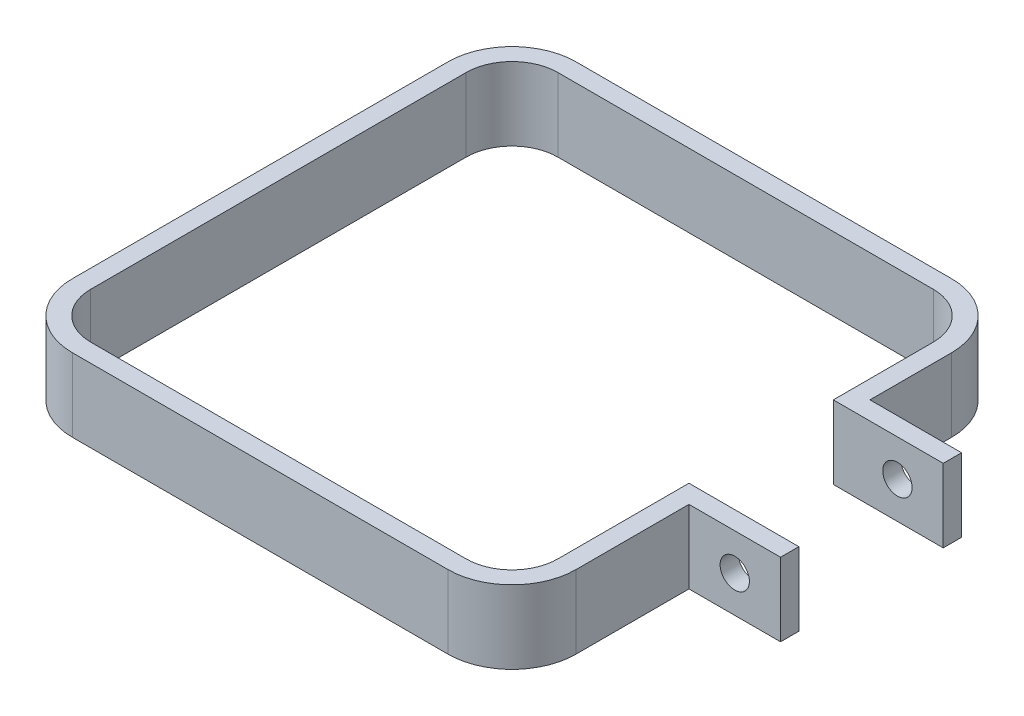
SolidWorks part; units mm, degrees
ref_plane "Front Plane" through (0, 0, 0) normal (0, 0, 1) x (1, 0, 0)
ref_plane "Top Plane" through (0, 0, 0) normal (0, 1, 0) x (1, 0, 0)
ref_plane "Right Plane" through (0, 0, 0) normal (1, 0, 0) x (0, 0, -1)
sketch "Sketch1" plane through (0, 0, 0) normal (0, 1, 0) x (1, 0, 0)
  line L0 (-20.5, 27.5) -> (20.5, 27.5)
  line L1 (-20.5, 25.5) -> (20.5, 25.5)
  line L2 (-25.5, 20.5) -> (-25.5, -20.5)
  line L3 (-20.5, -25.5) -> (20.5, -25.5)
  line L4 (25.5, 20.5) -> (25.5, 9.5842)
  line L5 (-25.5, 25.5) -> (25.5, -25.5) construction
  line L6 (-25.5, -25.5) -> (25.5, 25.5) construction
  line L7 (27.5, 20.5) -> (27.5, 11.5842)
  line L8 (-20.5, -27.5) -> (20.5, -27.5)
  line L9 (-27.5, 20.5) -> (-27.5, -20.5)
  line L10 (27.5, 11.5842) -> (37.5, 11.5842)
  line L11 (37.5, 11.5842) -> (37.5, 9.5842)
  line L12 (37.5, 9.5842) -> (27.5, 9.5842)
  line L13 (27.5, -6.178) -> (37.5, -6.178)
  line L14 (37.5, -6.178) -> (37.5, -8.178)
  line L15 (37.5, -8.178) -> (27.5, -8.178)
  line L16 (27.5, -8.178) -> (27.5, -20.5)
  line L17 (27.5, 9.5842) -> (25.5, 9.5842)
  line L18 (27.5, 20.5) -> (27.5, -20.5) construction
  line L19 (27.5, -6.178) -> (25.5, -6.178)
  line L20 (25.5, -6.178) -> (25.5, -20.5)
  line L22 (25.5, 20.5) -> (25.5, -20.5) construction
  arc A0 (20.5, -25.5) -> (25.5, -20.5) centre (20.5, -20.5) ccw
  arc A1 (-20.5, -25.5) -> (-25.5, -20.5) centre (-20.5, -20.5) cw
  arc A2 (25.5, 20.5) -> (20.5, 25.5) centre (20.5, 20.5) ccw
  arc A3 (-20.5, 25.5) -> (-25.5, 20.5) centre (-20.5, 20.5) ccw
  arc A4 (27.5, 20.5) -> (20.5, 27.5) centre (20.5, 20.5) ccw
  arc A5 (20.5, -27.5) -> (27.5, -20.5) centre (20.5, -20.5) ccw
  arc A6 (-20.5, -27.5) -> (-27.5, -20.5) centre (-20.5, -20.5) cw
  arc A7 (-20.5, 27.5) -> (-27.5, 20.5) centre (-20.5, 20.5) ccw
  point P0 (0, 0)
  dimension "D3" = 5
  dimension "D1" = 51
  dimension "D2" = 51
  dimension "D5" = 2
  dimension "D6" = 2
  dimension "D7" = 10
  dimension "D8" = 10
  dimension "D4" = 2
extrude "Boss-Extrude1" add sketch "Sketch1" along normal blind 8
sketch "Sketch2" plane through (0, 0, -11.5842) normal (0, 0, -1) x (-1, 0, 0)
  line L0 (-32.5, 8) -> (-32.5, 0) construction
  line L1 (-37.5, 8) -> (-27.5, 8) construction
  line L2 (-37.5, 0) -> (-27.5, 0) construction
  line L3 (-37.5, 4) -> (-27.5, 4) construction
  line L4 (-37.5, 8) -> (-37.5, 0) construction
  line L5 (-27.5, 8) -> (-27.5, 0) construction
  circle A0 centre (-32.5, 4) radius 1.6
  dimension "D1" = 3.2
extrude "Cut-Extrude1" cut sketch "Sketch2" against normal up to surface (37.0842 mm away)
